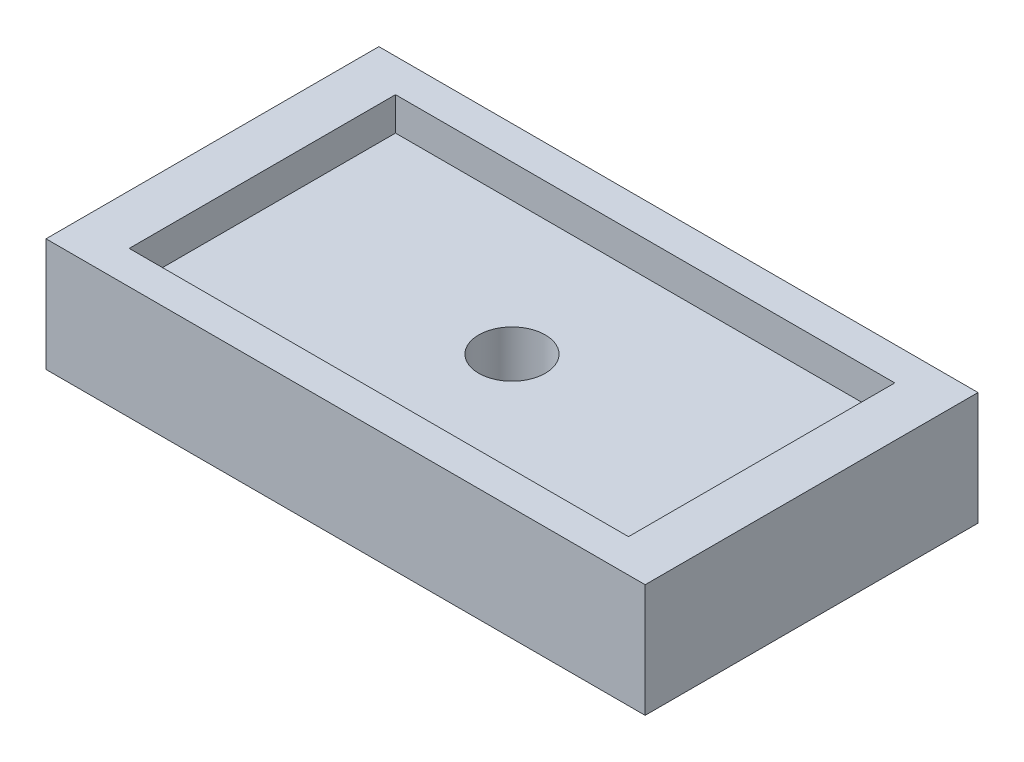
SolidWorks part; units mm, degrees
ref_plane "Front Plane" through (0, 0, 0) normal (0, 0, 1) x (1, 0, 0)
ref_plane "Top Plane" through (0, 0, 0) normal (0, 1, 0) x (1, 0, 0)
ref_plane "Right Plane" through (0, 0, 0) normal (1, 0, 0) x (0, 0, -1)
sketch "Sketch1" plane through (0, 0, 0) normal (0, 1, 0) x (1, 0, 0)
  line L1 (0, 0) -> (90, 0)
  line L2 (0, 0) -> (0, 50)
  line L3 (0, 50) -> (90, 50)
  line L4 (90, 0) -> (90, 50)
  dimension "D1" = 90
  dimension "D2" = 50
extrude "Boss-Extrude1" add sketch "Sketch1" along normal blind 17
sketch "Sketch2" plane through (0, 17, 0) normal (0, 1, 0) x (1, 0, 0)
  line L0 (0, 0) -> (90, 0) construction
  line L1 (7.5, 5) -> (82.5, 5)
  line L2 (7.5, 5) -> (7.5, 45)
  line L3 (7.5, 45) -> (82.5, 45)
  line L4 (82.5, 5) -> (82.5, 45)
  line L5 (0, 50) -> (0, 0) construction
  dimension "D1" = 5
  dimension "D2" = 40
  dimension "D3" = 7.5
  dimension "D4" = 75
extrude "Cut-Extrude1" cut sketch "Sketch2" against normal blind 5
sketch "Sketch3" plane through (0, 12, 0) normal (0, 1, 0) x (1, 0, 0)
  line L0 (7.5, 45) -> (82.5, 5) construction
  circle A0 centre (45, 25) radius 5
  dimension "D1" = 10
extrude "Cut-Extrude2" cut sketch "Sketch3" against normal through all
